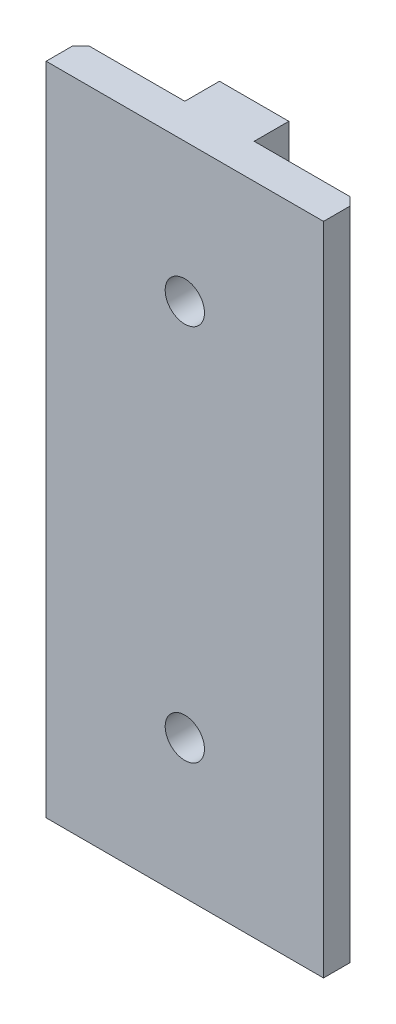
SolidWorks part; units mm, degrees
ref_plane "Front Plane" through (0, 0, 0) normal (0, 0, 1) x (1, 0, 0)
ref_plane "Top Plane" through (0, 0, 0) normal (0, 1, 0) x (1, 0, 0)
ref_plane "Right Plane" through (0, 0, 0) normal (1, 0, 0) x (0, 0, -1)
sketch "Sketch1" plane through (0, 0, 0) normal (0, 1, 0) x (1, 0, 0)
  line L0 (-3.175, 6.35) -> (3.175, 6.35)
  line L1 (12.7, 0) -> (-12.7, 0)
  line L2 (12.7, 0) -> (12.7, 3.175)
  line L3 (12.7, 3.175) -> (3.175, 3.175)
  line L4 (-12.7, 0) -> (-12.7, 3.175)
  line L7 (-3.175, 6.35) -> (-3.175, 3.175)
  line L8 (3.175, 6.35) -> (3.175, 3.175)
  line L12 (-3.175, 3.175) -> (-12.7, 3.175)
  point P0 (0, 0)
  point P6 (0, 6.35)
  point P7 (0, 0)
  dimension "D1" = 25.4
  dimension "D2" = 3.175
  dimension "D3" = 3.175
  dimension "D4" = 6.35
extrude "Boss-Extrude1" add sketch "Sketch1" along normal blind 60
sketch "Sketch2" plane through (0, 0, -6.35) normal (0, 0, -1) x (-1, 0, 0)
  line L0 (0, 60) -> (0, 0) construction
  line L1 (-3.175, 60) -> (3.175, 60) construction
  line L2 (-3.175, 0) -> (3.175, 0) construction
  circle A0 centre (0, 12.7) radius 8
  circle A1 centre (0, 47.3) radius 8
  circle A2 centre (0, 47.3) radius 1.5
  circle A3 centre (0, 12.7) radius 1.5
  dimension "D1" = 12.7
  dimension "D2" = 12.7
extrude "Cut-Extrude2" cut sketch "Sketch2" against normal through all contours L0 A2 | A2 L0 | A3 L0 | L0 A3
hole_wizard "CSK for M3 SFHCS1" positions "3DSketch1" profile "Sketch4" countersink size "M3" standard "ANSI Metric" end condition through all
sketch3d "3DSketch1"
  line L0 (0, 12.7, 0) -> (0, 12.7, -6.35) construction
  line L1 (0, 47.3, 0) -> (0, 47.3, -6.35) construction
  point P0 (0, 12.7, -6.35)
  point P4 (0, 47.3, -6.35)
sketch "Sketch4" plane through (0, 12.7, -6.35) normal (1, 0, 0) x (0, 1, 0)
  line L0 (0, 0) -> (0, 6.35)
  line L1 (0, 6.35) -> (1.8, 6.35)
  line L2 (1.8, 6.35) -> (1.8, 2.83)
  line L3 (1.8, 2.83) -> (3.36, 1.27)
  line L4 (3.36, 1.27) -> (3.36, 0)
  line L6 (3.36, 0) -> (0, 0)
  line L7 (-1.8, 2.83) -> (-3.36, 1.27) construction
  line L11 (0, -6.35) -> (0, 107.95) construction
  dimension "Thru Hole Dia." = 3.6
  dimension "Thru Hole Depth" = 6.35
  dimension "C'Sink Dia." = 6.72
  dimension "C'Sink Angle" = 90
  dimension "Head Clearance" = 1.27
chamfer "Chamfer1" distance 0.762 angle 45 2 edges at (12.7, 30, -3.175) (-12.7, 30, -3.175)
